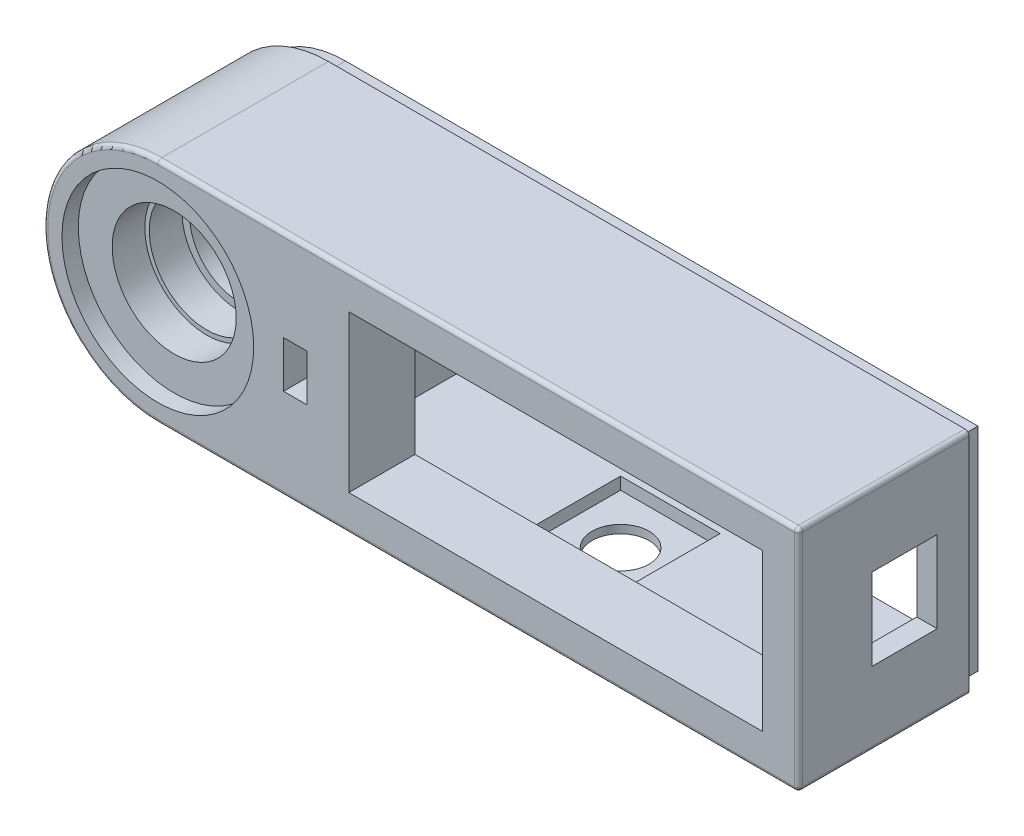
SolidWorks part; units mm, degrees
ref_plane "Спереди" through (0, 0, 0) normal (0, 0, 1) x (1, 0, 0)
ref_plane "Сверху" through (0, 0, 0) normal (0, 1, 0) x (1, 0, 0)
ref_plane "Справа" through (0, 0, 0) normal (1, 0, 0) x (0, 0, -1)
sketch "Эскиз1" plane through (0, 0, 0) normal (0, 0, 1) x (1, 0, 0)
  line L1 (39.25, -14) -> (-39.25, -14)
  line L2 (39.25, -14) -> (39.25, 14)
  line L3 (39.25, 14) -> (-39.25, 14)
  line L4 (-39.25, -14) -> (-39.25, 14) construction
  line L5 (39.25, -14) -> (-39.25, 14) construction
  line L6 (39.25, 14) -> (-39.25, -14) construction
  arc A0 (-39.25, 14) -> (-39.25, -14) centre (-39.25, 0) ccw
  point P1 (0, 0)
  dimension "D1" = 14
  dimension "D2" = 78.5
extrude "Бобышка-Вытянуть1" add sketch "Эскиз1" along normal blind 23
sketch "Эскиз2" plane through (0, 0, 23) normal (0, 0, 1) x (1, 0, 0)
  circle A0 centre (-39.25, 0) radius 11.75
  dimension "D1" = 23.5
extrude "Вырез-Вытянуть1" cut sketch "Эскиз2" against normal blind 2
sketch "Эскиз3" plane through (0, 0, 21) normal (0, 0, 1) x (1, 0, 0)
  circle A0 centre (-39.25, 0) radius 7.6
  dimension "D1" = 15.2
extrude "Вырез-Вытянуть2" cut sketch "Эскиз3" against normal blind 4
sketch "Эскиз4" plane through (0, 0, 17) normal (0, 0, 1) x (1, 0, 0)
  circle A0 centre (-39.25, 0) radius 7.05
  dimension "D1" = 14.1
extrude "Вырез-Вытянуть3" cut sketch "Эскиз4" against normal blind 4
sketch "Эскиз5" plane through (0, 0, 13) normal (0, 0, 1) x (1, 0, 0)
  circle A0 centre (-39.25, 0) radius 6.1
  dimension "D1" = 12.2
extrude "Вырез-Вытянуть4" cut sketch "Эскиз5" against normal blind 4
sketch "Эскиз6" plane through (0, 0, 9) normal (0, 0, 1) x (1, 0, 0)
  circle A0 centre (-39.25, 0) radius 2.6
  dimension "D1" = 5.2
extrude "Вырез-Вытянуть5" cut sketch "Эскиз6" against normal blind 9
sketch "Эскиз7" plane through (0, 0, 0) normal (0, 0, -1) x (-1, 0, 0)
  circle A0 centre (39.25, 0) radius 2.95
  dimension "D1" = 5.9
extrude "Вырез-Вытянуть6" cut sketch "Эскиз7" against normal blind 1.1
sketch "Эскиз8" plane through (0, 0, 23) normal (0, 0, 1) x (1, 0, 0)
  line L0 (-53.25, 0) -> (39.25, 0) construction
  line L1 (-15.85, 9.6) -> (34.85, 9.6)
  line L2 (-15.85, 9.6) -> (-15.85, -9.6)
  line L3 (-15.85, -9.6) -> (34.85, -9.6)
  line L4 (34.85, 9.6) -> (34.85, -9.6)
  line L5 (39.25, -14) -> (39.25, 14) construction
  line L6 (-39.25, -14) -> (39.25, -14) construction
  arc A0 (-39.25, 14) -> (-39.25, -14) centre (-39.25, 0) ccw construction
  point P12 (-15.85, 0)
  dimension "D1" = 19.2
  dimension "D2" = 50.7
  dimension "D3" = 4.4
  dimension "D4" = 4.4
extrude "Вырез-Вытянуть7" cut sketch "Эскиз8" against normal blind 8.1
sketch "Эскиз9" plane through (0, 0, 0) normal (0, 0, -1) x (-1, 0, 0)
  line L0 (-39.25, 0) -> (53.25, 0) construction
  line L1 (-39.25, -14) -> (-39.25, 14) construction
  line L2 (-36.75, -11.5) -> (-39.25, -11.5) construction
  line L3 (-36.75, 11.5) -> (23.75, 11.5)
  line L4 (-36.75, 11.5) -> (-36.75, -11.5)
  line L5 (-36.75, -11.5) -> (23.75, -11.5)
  line L6 (23.75, 11.5) -> (23.75, -11.5)
  line L7 (-36.75, -11.5) -> (-36.75, -14) construction
  line L8 (39.25, -14) -> (-39.25, -14) construction
  line L9 (-36.75, 11.5) -> (-36.75, 14) construction
  line L10 (-39.25, 14) -> (39.25, 14) construction
  circle A0 centre (39.25, 0) radius 14 construction
  point P11 (-36.75, 0)
  dimension "D1" = 2.5
  dimension "D2" = 15.5
extrude "Вырез-Вытянуть8" cut sketch "Эскиз9" against normal up to surface (14.9 mm away) up to face at (9.5, 0, 14.9)
sketch "Эскиз10" plane through (39.25, 0, 0) normal (1, 0, 0) x (0, 0, -1)
  line L0 (-23, -14) -> (-23, 14) construction
  line L1 (-14, -5) -> (-6, -5)
  line L2 (-14, -5) -> (-14, 5)
  line L3 (-14, 5) -> (-6, 5)
  line L4 (-6, -5) -> (-6, 5)
  line L5 (-14, -5) -> (-6, 5) construction
  line L6 (-14, 5) -> (-6, -5) construction
  point P0 (-10, 0)
  point P11 (-23, 0)
  dimension "D1" = 17
  dimension "D3" = 8
  dimension "D4" = 10
extrude "Вырез-Вытянуть9" cut sketch "Эскиз10" against normal up to next
sketch "Эскиз11" plane through (0, 0, 0) normal (0, 0, -1) x (-1, 0, 0)
  line L6 (39.25, 13) -> (-38.25, 13)
  line L7 (-38.25, 13) -> (-38.25, -13)
  line L8 (-38.25, -13) -> (39.25, -13)
  line L9 (39.25, 13) -> (-38.25, 13)
  line L10 (-38.25, 13) -> (-38.25, -13)
  line L11 (-38.25, -13) -> (39.25, -13)
  arc A2 (39.25, -13) -> (39.25, 13) centre (39.25, 0) ccw
  arc A3 (39.25, -13) -> (39.25, 13) centre (39.25, 0) ccw
  dimension "D1" = 1
extrude "Вырез-Вытянуть-Тонкостенный1" cut sketch "Эскиз11" against normal blind 2.1 thin
sketch "Эскиз13" plane through (0, -11.5, 0) normal (0, 1, 0) x (1, 0, 0)
  line L1 (-2.85, -14.9) -> (9.35, -14.9)
  line L2 (-2.85, -14.9) -> (-2.85, -2.7)
  line L3 (-2.85, -2.7) -> (9.35, -2.7)
  line L4 (9.35, -14.9) -> (9.35, -2.7)
  line L5 (-2.85, -14.9) -> (9.35, -2.7) construction
  line L6 (-2.85, -2.7) -> (9.35, -14.9) construction
  line L7 (36.75, -14.9) -> (-23.75, -14.9) construction
  point P8 (3.25, -8.8)
  point P9 (0, 0)
  dimension "D1" = 12.2
extrude "Вырез-Вытянуть11" cut sketch "Эскиз13" against normal offset from surface (1.5 mm away) 1 up to face at (0, -14, 12.55)
sketch "Эскиз16" plane through (0, -13, 0) normal (0, 1, 0) x (1, 0, 0)
  line L0 (9.35, -2.7) -> (-2.85, -14.9) construction
  line L1 (9.35, -14.9) -> (-2.85, -2.7) construction
  circle A0 centre (3.25, -8.8) radius 3.5
  point P8 (3.25, -8.8)
  dimension "D1" = 7
extrude "Вырез-Вытянуть14" cut sketch "Эскиз16" against normal up to next
sketch "Эскиз14" plane through (0, 0, 14.9) normal (0, 0, -1) x (-1, 0, 0)
  line L0 (15.85, 9.6) -> (15.85, -9.6) construction
  line L1 (23.75, -2.75) -> (21.05, -2.75)
  line L2 (23.75, -2.75) -> (23.75, 2.75)
  line L3 (23.75, 2.75) -> (21.05, 2.75)
  line L4 (21.05, -2.75) -> (21.05, 2.75)
  line L5 (23.75, -2.75) -> (21.05, 2.75) construction
  line L6 (23.75, 2.75) -> (21.05, -2.75) construction
  line L7 (23.75, -11.5) -> (23.75, 11.5) construction
  point P0 (22.4, 0)
  point P9 (15.85, 0)
  dimension "D1" = 5.5
  dimension "D2" = 2.7
extrude "Вырез-Вытянуть12" cut sketch "Эскиз14" against normal blind 12
sketch "Эскиз15" plane through (0, 0, 23) normal (0, 0, 1) x (1, 0, 0)
  line L8 (-23.85, -2.85) -> (-20.95, -2.85)
  line L9 (-23.85, 2.85) -> (-23.85, -2.85)
  line L10 (-20.95, 2.85) -> (-23.85, 2.85)
  line L11 (-20.95, -2.85) -> (-20.95, 2.85)
  line L12 (-23.85, -2.85) -> (-20.95, -2.85)
  line L13 (-23.85, 2.85) -> (-23.85, -2.85)
  line L14 (-20.95, 2.85) -> (-23.85, 2.85)
  line L15 (-20.95, -2.85) -> (-20.95, 2.85)
  dimension "D1" = 0.1
extrude "Вырез-Вытянуть13" cut sketch "Эскиз15" against normal offset from surface (5.6 mm away) 2.5 up to face at (9.5, 0, 14.9)
fillet "Скругление1" radius 0.5 6 edges at (0, -14, 23) (-53.25, 0, 23) (0, 14, 23) (39.25, 0, 23) (39.25, -14, 12.55) (39.25, 14, 12.55)
